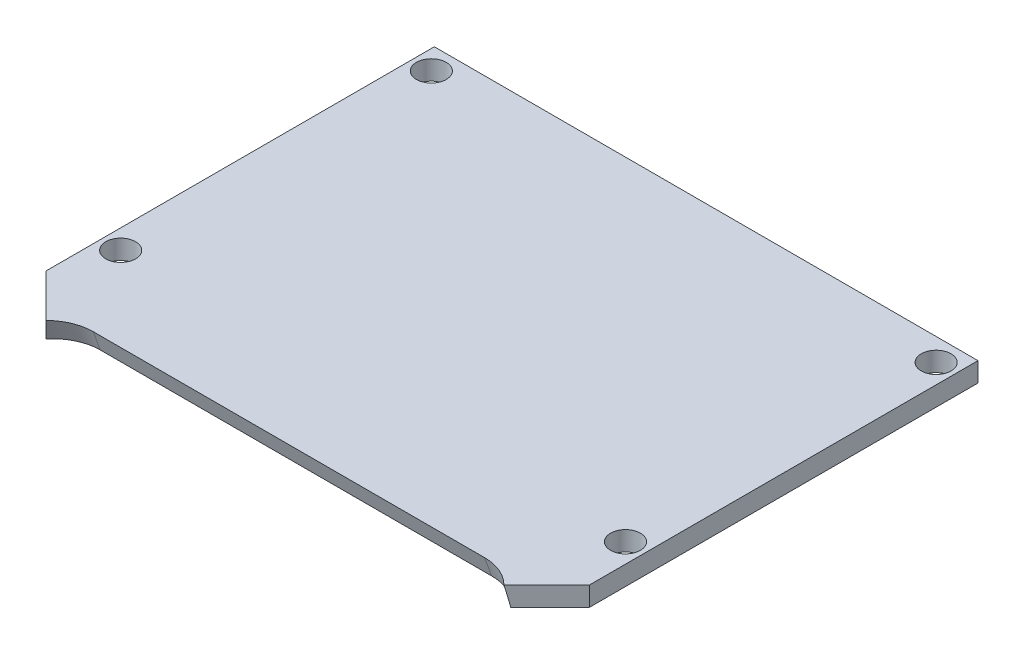
SolidWorks part; units mm, degrees
material "Acrylic (Medium-high impact)"
ref_plane "Front Plane" through (0, 0, 0) normal (0, 0, 1) x (1, 0, 0)
ref_plane "Top Plane" through (0, 0, 0) normal (0, 1, 0) x (1, 0, 0)
ref_plane "Right Plane" through (0, 0, 0) normal (1, 0, 0) x (0, 0, -1)
sketch "Sketch1" plane through (0, 0, 0) normal (0, 1, 0) x (1, 0, 0)
  line L0 (-22.225, 0) -> (0, -22.225)
  line L1 (-22.225, 31.75) -> (22.225, 31.75)
  line L2 (-22.225, 31.75) -> (-22.225, 0)
  line L4 (22.225, 31.75) -> (22.225, 0)
  line L5 (0, -22.225) -> (22.225, 0)
  dimension "D1" = 44.45
  dimension "D2" = 31.75
extrude "Boss-Extrude1" add sketch "Sketch1" along normal blind 1.5875
extrude "Cut-Extrude3" cut sketch "Sketch4" along normal through all
sketch "Sketch4" plane through (0, 17.6223, -73.2933) normal (0, 0.9397, 0.342) x (1, 0, 0)
  line L6 (0, -95.785) -> (18.9972, -77.9335)
  line L7 (-18.9972, -77.9335) -> (0, -95.785)
  line L8 (16, -76.5824) -> (-16, -76.5824)
  arc A2 (-16, -76.5824) -> (-18.9972, -77.9335) centre (-16, -80.5824) ccw
  arc A3 (18.9972, -77.9335) -> (16, -76.5824) centre (16, -80.5824) ccw
hole_wizard "#2 Clearance Hole1" positions "Sketch5" profile "Sketch6" hole size "#2" standard "ANSI Inch" end condition through all
sketch "Sketch5" plane through (0, 1.5875, 5.1744) normal (0, 1, 0) x (0, 0, 1)
  point P0 (-9.6905, 20.6375)
  point P2 (-35.0905, 20.6375)
  point P4 (-35.0905, -20.6375)
  point P6 (-9.6905, -20.6375)
  point P9 (0, 0)
  point P12 (0, 0)
  point P15 (0, 0)
  point P16 (0, 0)
  point P19 (0, 0)
  point P20 (0, 0)
sketch "Sketch6" plane through (20.6375, 1.5875, -4.5161) normal (1, 0, 0) x (0, 0, 1)
  line L0 (0, 0) -> (0, 1.5875)
  line L1 (0, 1.5875) -> (1.2192, 1.5875)
  line L2 (1.2192, 1.5875) -> (1.2192, 0)
  line L3 (1.2192, 0) -> (0, 0)
  line L4 (0, -6.35) -> (0, 107.95) construction
  dimension "Thru Hole Dia." = 2.4384
  dimension "Thru Hole Depth" = 1.5875
